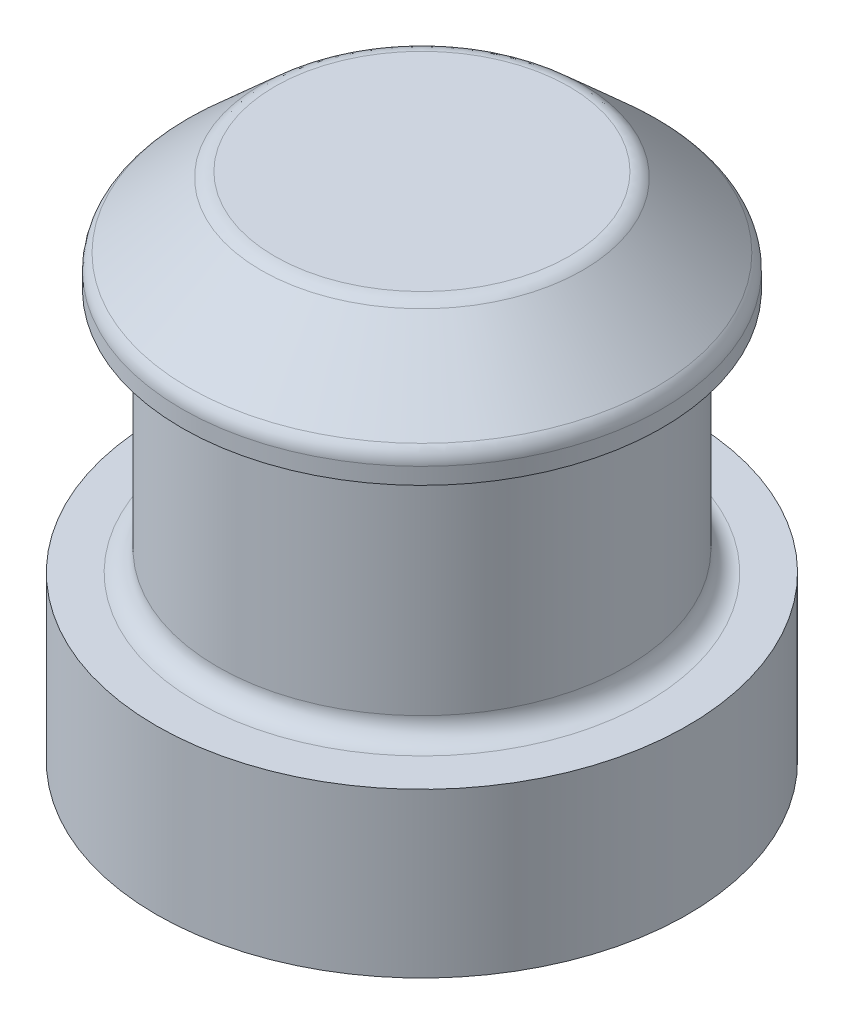
SolidWorks part; units mm, degrees
ref_plane "Front Plane" through (0, 0, 0) normal (0, 0, 1) x (1, 0, 0)
ref_plane "Top Plane" through (0, 0, 0) normal (0, 1, 0) x (1, 0, 0)
ref_plane "Right Plane" through (0, 0, 0) normal (1, 0, 0) x (0, 0, -1)
sketch "Sketch1" plane through (0, 0, 0) normal (0, 1, 0) x (1, 0, 0)
  line L5 (7, -7) -> (-7, 7) construction
  line L6 (7, 7) -> (-7, -7) construction
  circle A0 centre (0, 0) radius 2.6
  point P0 (0, 0)
  dimension "D3" = 5.2
  dimension "D1" = 14
  dimension "D2" = 14
extrude "Boss-Extrude1" add sketch "Sketch1" along normal blind 1.6
ref_plane "Plane1" through (0, 1.6, 0) normal (0, 1, 0) x (1, 0, 0)
sketch "Sketch2" plane through (0, 1.6, 0) normal (0, 1, 0) x (1, 0, 0)
  circle A0 centre (0, 0) radius 2
extrude "Boss-Extrude2" add sketch "Sketch2" along normal blind 2.4
ref_plane "Plane2" through (0, 4, 0) normal (0, 1, 0) x (1, 0, 0)
sketch "Sketch3" plane through (0, 4, 0) normal (0, 1, 0) x (1, 0, 0)
  circle A0 centre (0, 0) radius 2.35
  circle A1 centre (0, 0) radius 2 construction
extrude "Boss-Extrude3" add sketch "Sketch3" along normal blind 1
chamfer "Chamfer1" distance 0.75 angle 48 1 edges at (0, 5, 2.35)
fillet "Fillet1" radius 0.2 3 edges at (0, 5, 1.517) (0, 4.25, 2.35) (0, 1.6, 2)
scale "Scale1" scale about centroid uniform scaling yes scale factor 1.15
